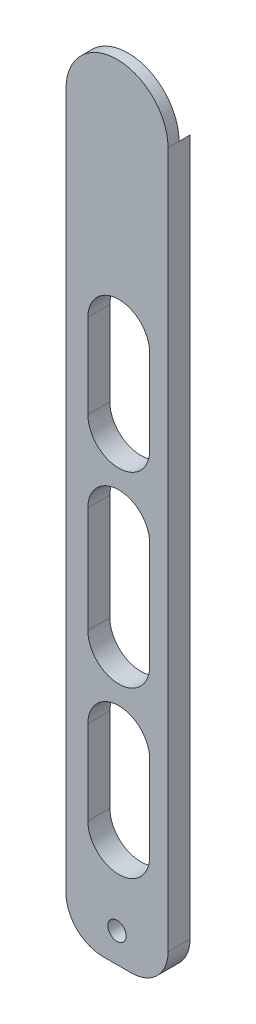
SolidWorks part; units mm, degrees
ref_plane "Plan de face" through (0, 0, 0) normal (0, 0, 1) x (1, 0, 0)
ref_plane "Plan de dessus" through (0, 0, 0) normal (0, 1, 0) x (1, 0, 0)
ref_plane "Plan de droite" through (0, 0, 0) normal (1, 0, 0) x (0, 0, -1)
sketch "Esquisse1" plane through (0, 0, 0) normal (0, 0, 1) x (1, 0, 0)
  line L1 (-9.8138, 31.7623) -> (18.0362, 31.7623)
  line L2 (-9.8138, 31.7623) -> (-9.8138, -168.2377)
  line L3 (-9.8138, -168.2377) -> (18.0362, -168.2377)
  line L4 (18.0362, 31.7623) -> (18.0362, -168.2377)
  arc A1 (18.0362, 31.7623) -> (-9.8138, 31.7623) centre (4.1112, 31.7623) ccw
  dimension "D1" = 27.85
  dimension "D2" = 200
extrude "Boss.-Extru.1" add sketch "Esquisse1" along normal blind 6 contours L4 L1 L2 L3 | L1 A1
sketch "Esquisse2" plane through (0, 0, 6) normal (0, 0, 1) x (1, 0, 0)
  line L0 (18.0362, 31.7623) -> (18.0362, -168.2377) construction
  line L1 (-5.6388, 41.5123) -> (13.8612, 41.5123)
  line L2 (-5.6388, 41.5123) -> (-5.6388, 1.0123)
  line L3 (-5.6388, 1.0123) -> (13.8612, 1.0123)
  line L4 (13.8612, 41.5123) -> (13.8612, 1.0123)
  circle A0 centre (4.1112, 31.7623) radius 2.925
  circle A1 centre (-0.9088, -0.8377) radius 1.5
  circle A2 centre (9.1312, -0.8377) radius 1.5
  arc A3 (18.0362, 31.7623) -> (-9.8138, 31.7623) centre (4.1112, 31.7623) ccw construction
  dimension "D4" = 9.75
  dimension "D5" = 5.85
  dimension "D6" = 1.85
  dimension "D7" = 1.85
  dimension "D8" = 3
  dimension "D9" = 3
  dimension "D1" = 19.5
  dimension "D2" = 40.5
  dimension "D3" = 4.175
  dimension "D10" = 4.73
  dimension "D11" = 4.73
sketch "Esquisse4" plane through (0, 0, 6) normal (0, 0, 1) x (1, 0, 0)
  line L0 (18.0362, 31.7623) -> (18.0362, -168.2377) construction
  line L1 (-9.8138, -168.2377) -> (18.0362, -168.2377) construction
  circle A0 centre (4.1112, -160.2377) radius 2.5
  dimension "D1" = 5
  dimension "D2" = 13.925
  dimension "D3" = 8
extrude "Enlèv. mat.-Extru.3" cut sketch "Esquisse4" against normal blind 29
sketch "Esquisse5" plane through (0, 0, 0) normal (0, 0, -1) x (-1, 0, 0)
  circle A0 centre (-4.1112, 31.7623) radius 13.925
extrude "Enlèv. mat.-Extru.4" cut sketch "Esquisse5" against normal blind 3
sketch "Esquisse6" plane through (0, 0, 0) normal (0, 0, -1) x (-1, 0, 0)
  line L0 (-9.6613, 18.9911) -> (-18.0362, -0.2801)
  line L1 (-18.0362, 31.7623) -> (-18.0362, -168.2377) construction
  line L2 (-18.0362, -0.2801) -> (-18.0362, 31.7623)
  arc A0 (-18.0362, 31.7623) -> (9.8138, 31.7623) centre (-4.1112, 31.7623) ccw construction
  arc A1 (-18.0362, 31.7623) -> (9.8138, 31.7623) centre (-4.1112, 31.7623) ccw construction
  arc A2 (-18.0362, 31.7623) -> (-9.6613, 18.9911) centre (-4.1112, 31.7623) ccw
extrude "Enlèv. mat.-Extru.5" [suppressed] cut sketch "Esquisse6" against normal blind 3
sketch "Esquisse7" plane through (0, 0, 0) normal (0, 0, -1) x (-1, 0, 0)
  line L1 (-13.0362, -115.2377) -> (3.8338, -115.2377)
  line L2 (-13.0362, -115.2377) -> (-13.0362, -138.2377)
  line L3 (-13.0362, -138.2377) -> (3.8338, -138.2377)
  line L4 (3.8338, -115.2377) -> (3.8338, -138.2377)
  line L5 (-18.0362, 31.7623) -> (-18.0362, -168.2377) construction
  line L6 (9.8138, -168.2377) -> (-18.0362, -168.2377) construction
  line L8 (3.8338, -93.2377) -> (-13.0362, -93.2377)
  line L9 (3.8338, -93.2377) -> (3.8338, -64.2377)
  line L10 (3.8338, -64.2377) -> (-13.0362, -64.2377)
  line L11 (-13.0362, -93.2377) -> (-13.0362, -64.2377)
  line L12 (3.8338, -19.2377) -> (-13.0362, -19.2377)
  line L13 (3.8338, -19.2377) -> (3.8338, -42.2377)
  line L14 (3.8338, -42.2377) -> (-13.0362, -42.2377)
  line L15 (-13.0362, -19.2377) -> (-13.0362, -42.2377)
  arc A0 (-13.0362, -138.2377) -> (3.8338, -138.2377) centre (-4.6012, -138.2377) ccw
  arc A1 (-13.0362, -115.2377) -> (3.8338, -115.2377) centre (-4.6012, -115.2377) cw
  arc A2 (-13.0362, -93.2377) -> (3.8338, -93.2377) centre (-4.6012, -93.2377) ccw
  arc A3 (3.8338, -64.2377) -> (-13.0362, -64.2377) centre (-4.6012, -64.2377) ccw
  arc A4 (3.8338, -42.2377) -> (-13.0362, -42.2377) centre (-4.6012, -42.2377) cw
  arc A5 (3.8338, -19.2377) -> (-13.0362, -19.2377) centre (-4.6012, -19.2377) ccw
  dimension "D1" = 16.87
  dimension "D2" = 5
  dimension "D3" = 30
  dimension "D4" = 147
  dimension "D5" = 29
  dimension "D6" = 22
  dimension "D7" = 23
  dimension "D8" = 22
extrude "Enlèv. mat.-Extru.6" cut sketch "Esquisse7" against normal blind 13 contours A1 L1 | L4 L1 L2 L3 | L3 A0 | L8 A2 | L11 L8 L9 L10 | L10 A3 | A4 L14 | L12 L15 L14 L13 | L12 A5
fillet "Congé1" radius 10 1 edges at (18.0362, -168.2377, 3)
fillet "Congé2" radius 10 1 edges at (-9.8138, -168.2377, 3)
